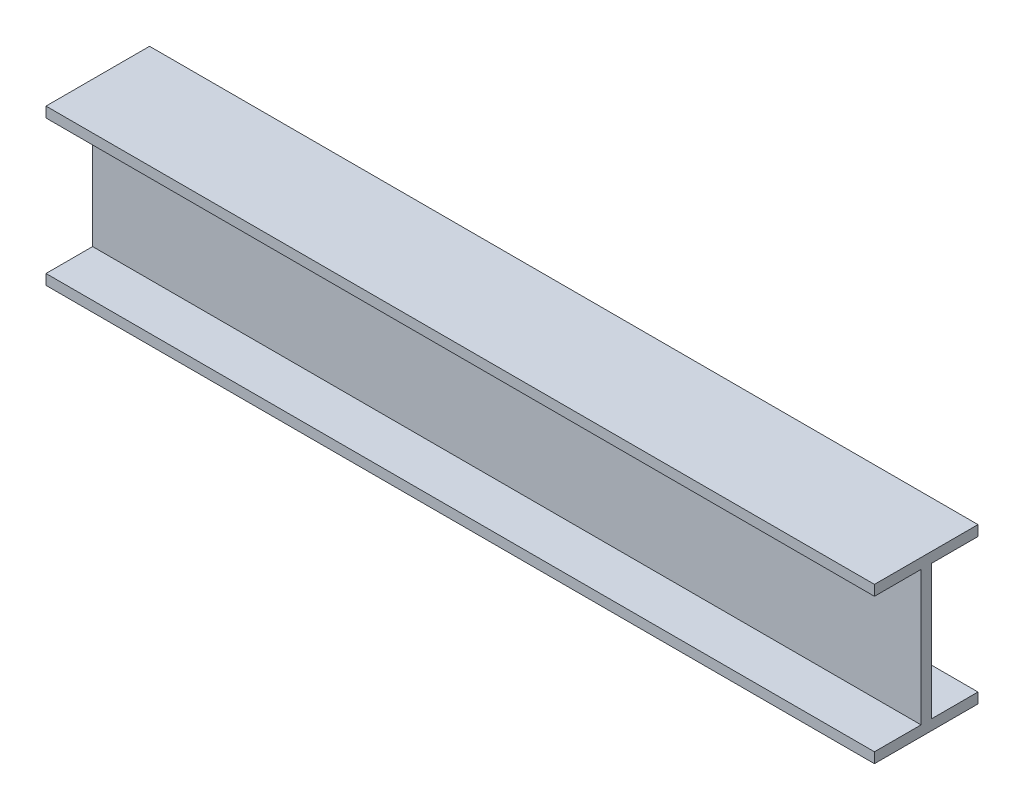
SolidWorks part; units mm, degrees
ref_plane "Front Plane" through (0, 0, 0) normal (0, 0, 1) x (1, 0, 0)
ref_plane "Top Plane" through (0, 0, 0) normal (0, 1, 0) x (1, 0, 0)
ref_plane "Right Plane" through (0, 0, 0) normal (1, 0, 0) x (0, 0, -1)
sketch "Sketch1" plane through (0, 0, 0) normal (1, 0, 0) x (0, 0, -1)
  line L0 (-50, 28.2563) -> (50, 28.2563)
  line L1 (50, 28.2563) -> (50, 18.2563)
  line L2 (50, 18.2563) -> (5, 18.2563)
  line L3 (5, 18.2563) -> (5, -111.7437)
  line L5 (0, 82.5) -> (0, -82.5) construction
  line L6 (-5, 18.2563) -> (-5, -111.7437)
  line L7 (-50, 18.2563) -> (-5, 18.2563)
  line L8 (-50, 28.2563) -> (-50, 18.2563)
  line L9 (55, -46.7437) -> (-55, -46.7437) construction
  line L10 (-50, -121.7437) -> (-50, -111.7437)
  line L11 (-50, -111.7437) -> (-5, -111.7437)
  line L12 (50, -111.7437) -> (5, -111.7437)
  line L13 (50, -121.7437) -> (50, -111.7437)
  line L14 (-50, -121.7437) -> (50, -121.7437)
  point P3 (0, 0)
  point P14 (0, 28.2563)
  point P17 (-5, -46.7437)
  point P19 (5, -46.7437)
  point P22 (0, -121.7437)
extrude "Boss-Extrude1" add sketch "Sketch1" along normal mid plane 800 contours L0 L1 L2 L3 L12 L13 L14 L10 L11 L6 L7 L8
